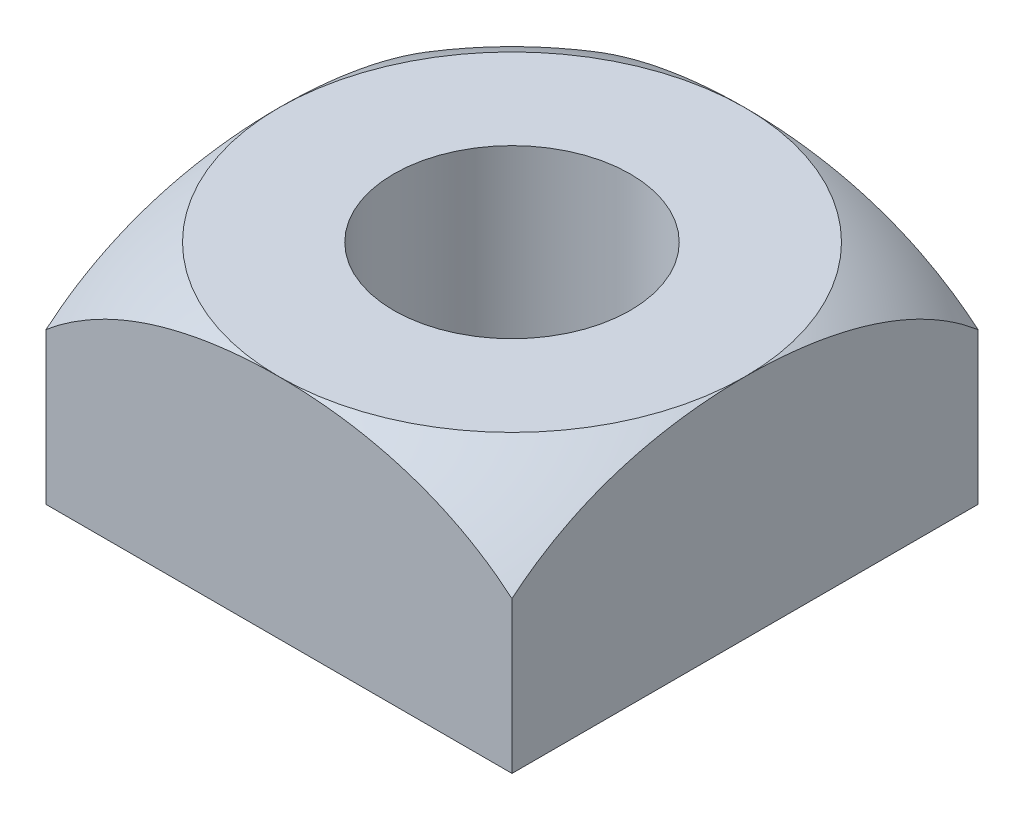
SolidWorks part; units mm, degrees
ref_plane "Front Plane" through (0, 0, 0) normal (0, 0, 1) x (1, 0, 0)
ref_plane "Top Plane" through (0, 0, 0) normal (0, 1, 0) x (1, 0, 0)
ref_plane "Right Plane" through (0, 0, 0) normal (1, 0, 0) x (0, 0, -1)
sketch "Sketch1" plane through (0, 0, 0) normal (0, 1, 0) x (1, 0, 0)
  line L1 (-4.925, -4.925) -> (4.925, -4.925)
  line L2 (-4.925, -4.925) -> (-4.925, 4.925)
  line L3 (-4.925, 4.925) -> (4.925, 4.925)
  line L4 (4.925, -4.925) -> (4.925, 4.925)
  line L5 (0, 4.925) -> (0, -4.925) construction
  line L6 (-4.925, 0) -> (4.925, 0) construction
  point P0 (0, 0)
  dimension "D1" = 9.85
extrude "Boss-Extrude1" add sketch "Sketch1" along normal blind 4.8
sketch "Sketch2" plane through (0, 0, 0) normal (0, 1, 0) x (1, 0, 0)
  circle A0 centre (0, 0) radius 2.5
  dimension "D1" = 5
extrude "Cut-Extrude2" cut sketch "Sketch2" against normal through all and the other way through all
sketch "Sketch4" plane through (0, 0, 0) normal (0, 0, 1) x (1, 0, 0)
  line L0 (2.3597, 5.0354) -> (7.4881, 5.0354) construction
  line L1 (7.4881, 5.0354) -> (7.4881, -0.093) construction
  line L2 (-4.925, 4.8) -> (4.925, 4.8) construction
  line L5 (4.3772, 5.0354) -> (7.4881, 5.0354)
  line L7 (0, 0) -> (0, 4.8) construction
  line L11 (7.4881, 5.0354) -> (7.4881, 2.4712)
  arc A0 (4.3772, 5.0354) -> (7.4881, 2.4712) centre (2.21, -0.763) cw
  point P5 (7.1454, 2.7902)
  point P6 (2.3597, 5.0354)
  point P12 (4.925, 4.8)
revolve "Cut-Revolve3" cut sketch "Sketch4" angle 360 about L7
